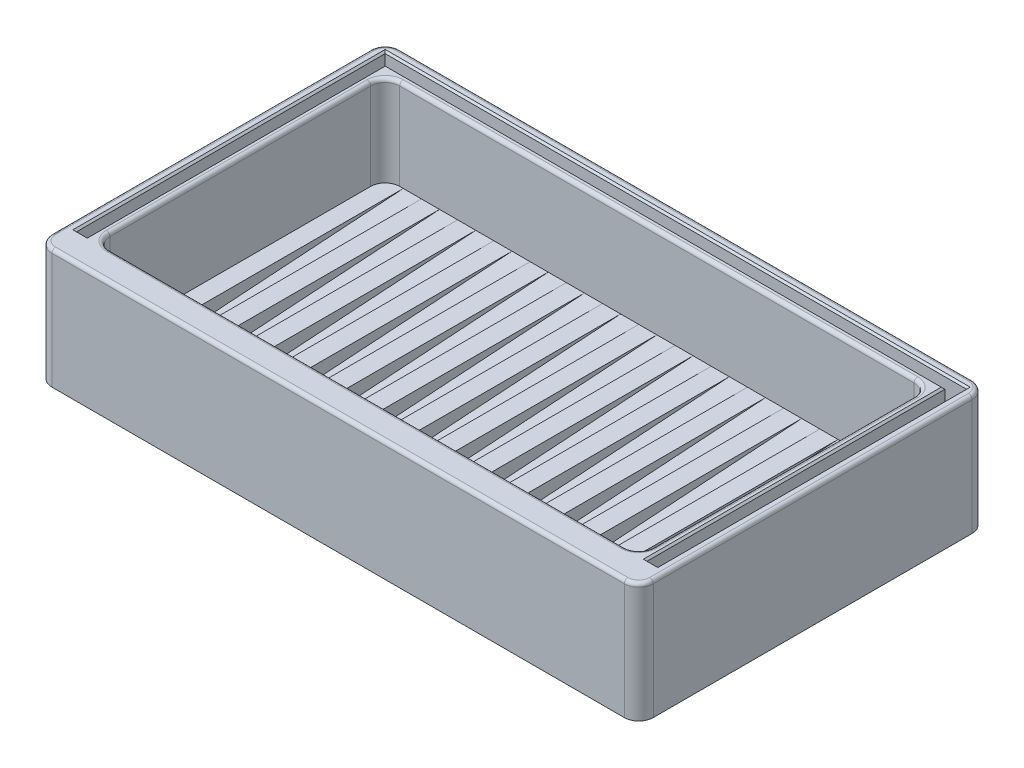
SolidWorks part; units mm, degrees
ref_plane "Front Plane" through (0, 0, 0) normal (0, 0, 1) x (1, 0, 0)
ref_plane "Top Plane" through (0, 0, 0) normal (0, 1, 0) x (1, 0, 0)
ref_plane "Right Plane" through (0, 0, 0) normal (1, 0, 0) x (0, 0, -1)
sketch "Sketch1" plane through (0, 0, 0) normal (0, 1, 0) x (1, 0, 0)
  line L1 (-64.9244, 29.2933) -> (101.0756, 29.2933)
  line L2 (-64.9244, 29.2933) -> (-64.9244, -66.7067)
  line L3 (-64.9244, -66.7067) -> (101.0756, -66.7067)
  line L4 (101.0756, 29.2933) -> (101.0756, -66.7067)
  dimension "D1" = 166
  dimension "D2" = 96
extrude "Boss-Extrude1" add sketch "Sketch1" along normal blind 33
sketch "Sketch2" plane through (0, 33, 0) normal (0, 1, 0) x (1, 0, 0)
  line L0 (101.0756, 29.2933) -> (-64.9244, 29.2933) construction
  line L1 (-56.9244, 21.2933) -> (93.0756, 21.2933)
  line L2 (-56.9244, 21.2933) -> (-56.9244, -58.7067)
  line L3 (-56.9244, -58.7067) -> (93.0756, -58.7067)
  line L4 (93.0756, 21.2933) -> (93.0756, -58.7067)
  line L5 (-64.9244, 29.2933) -> (-64.9244, -66.7067) construction
  dimension "D1" = 150
  dimension "D2" = 80
  dimension "D3" = 8
  dimension "D4" = 8
extrude "Cut-Extrude1" cut sketch "Sketch2" against normal blind 30
sketch "Sketch4" plane through (93.0756, 0, 0) normal (-1, 0, 0) x (0, 0, 1)
  line L0 (53.7067, 3) -> (-21.2933, 8)
  line L1 (58.7067, 3) -> (-21.2933, 3) construction
  line L2 (-21.2933, 8) -> (-21.2933, 3)
  line L3 (-21.2933, 3) -> (53.7067, 3)
  dimension "D1" = 5
  dimension "D2" = 5
extrude "Boss-Extrude2" add sketch "Sketch4" along normal blind 5
sketch "Sketch5" plane through (88.0756, 0, 0) normal (-1, 0, 0) x (0, 0, 1)
  line L0 (53.7067, 3) -> (53.7067, 8)
  line L1 (53.7067, 8) -> (-21.2933, 8)
  line L2 (-21.2933, 8) -> (-21.2933, 3)
  line L3 (-21.2933, 3) -> (53.7067, 3)
  dimension "D1" = 5
extrude "Boss-Extrude3" add sketch "Sketch5" along normal blind 5
pattern_linear "LPattern1" count 15 spacing 10 along (-1, 0, 0) of "Boss-Extrude2", "Boss-Extrude3"
sketch "Sketch9" plane through (0, 33, 0) normal (0, 1, 0) x (1, 0, 0)
  line L0 (101.0756, 29.2933) -> (-64.9244, 29.2933) construction
  line L1 (-62.1744, 26.5433) -> (98.3256, 26.5433)
  line L2 (-62.1744, 26.5433) -> (-62.1744, -58.7067)
  line L3 (-62.1744, -58.7067) -> (-59.1744, -58.7067)
  line L4 (98.3256, 26.5433) -> (98.3256, -58.7067)
  line L5 (-59.1744, 23.5433) -> (95.3256, 23.5433)
  line L6 (-59.1744, 23.5433) -> (-59.1744, -58.7067)
  line L8 (95.3256, 23.5433) -> (95.3256, -58.7067)
  line L9 (-64.9244, 29.2933) -> (-64.9244, -66.7067) construction
  line L10 (101.0756, -66.7067) -> (101.0756, 29.2933) construction
  line L11 (-64.9244, -66.7067) -> (101.0756, -66.7067) construction
  line L12 (95.3256, -58.7067) -> (98.3256, -58.7067)
  point P16 (0, 0)
  point P17 (0, 0)
  dimension "D1" = 3
  dimension "D2" = 3
  dimension "D4" = 3
  dimension "D5" = 2.75
  dimension "D6" = 2.75
  dimension "D7" = 2.75
  dimension "D8" = 8
extrude "Cut-Extrude5" cut sketch "Sketch9" against normal blind 10
fillet "Fillet1" radius 4 4 edges at (-64.9244, 16.5, -29.2933) (101.0756, 16.5, -29.2933) (101.0756, 16.5, 66.7067) (-64.9244, 16.5, 66.7067)
fillet "Fillet2" radius 4 4 edges at (93.0756, 18, 58.7067) (93.0756, 20.5, -21.2933) (-56.9244, 20.5, -21.2933) (-56.9244, 18, 58.7067)
fillet "Fillet3" radius 2 15 edges at (85.5756, 8, 53.7067) (75.5756, 8, 53.7067) (65.5756, 8, 53.7067) (55.5756, 8, 53.7067) (45.5756, 8, 53.7067) (35.5756, 8, 53.7067) (25.5756, 8, 53.7067) (15.5756, 8, 53.7067) (5.5756, 8, 53.7067) (-4.4244, 8, 53.7067) (-14.4244, 8, 53.7067) (-24.4244, 8, 53.7067) (-34.4244, 8, 53.7067) (-44.4244, 8, 53.7067) (-54.4244, 8, 53.7067)
fillet "Fillet5" radius 1 16 edges at (-55.7529, 33, 57.5351) (-56.9244, 33, 18.7067) (18.0756, 33, 58.7067) (91.904, 33, 57.5351) (93.0756, 33, 18.7067) (91.904, 33, -20.1217) (18.0756, 33, -21.2933) (-55.7529, 33, -20.1217) (-63.7529, 33, -28.1217) (18.0756, 33, -29.2933) (99.904, 33, -28.1217) (101.0756, 33, 18.7067) (99.904, 33, 65.5351) (18.0756, 33, 66.7067) (-64.9244, 33, 18.7067) (-63.7529, 33, 65.5351)
chamfer "Chamfer1" distance 0.5 angle 45 8 edges at (95.3256, 33, 17.5817) (96.8256, 33, 58.7067) (98.3256, 33, 16.0817) (18.0756, 33, -23.5433) (-59.1744, 33, 17.5817) (-60.6744, 33, 58.7067) (-62.1744, 33, 16.0817) (18.0756, 33, -26.5433)
equation "\"Inner width\"= 80"
equation "\"Inner length\" = 150"
equation "\"pannel thick\" = 2.5"
equation "\"base thickness\" = 3"
equation "\"D1@Sketch1\" = \"Inner length\" + \"Side thickness\" * 2"
equation "\"D2@Sketch1\" = \"Inner width\" + \"Side thickness\" * 2"
equation "\"Base inner height\"= 25"
equation "\"D1@Boss-Extrude1\"=\"Base inner height\"+\"base thickness\"+\"Drainage height\""
equation "\"D1@Sketch2\"=\"Inner length\""
equation "\"D2@Sketch2\"=\"Inner width\""
equation "\"D3@Sketch2\"=\"Side thickness\""
equation "\"D4@Sketch2\" = \"Side thickness\""
equation "\"Drainage height\" = 5"
equation "\"D1@Cut-Extrude1\"=\"Base inner height\"+\"Drainage height\""
equation "\"Side thickness\" = 8"
equation "\"D1@Sketch4\"=\"Drainage height\""
equation "\"Drainage gap\"= \"Inner length\" / \"Drain amount\""
equation "\"D2@Sketch4\"=\"Drainage gap\""
equation "\"D1@Boss-Extrude2\"=\"Drainage gap\""
equation "\"D1@Sketch5\"=\"Drainage height\""
equation "\"D3@LPattern1\"=\"Drainage gap\"*2"
equation "\"Drain amount\"= 30"
equation "\"pannel seat depth\"= 10"
equation "\"D1@Cut-Extrude5\"=\"pannel seat depth\""
equation "\"D8@Sketch9\"=\"Side thickness\""
equation "\"D1@Boss-Extrude3\"=\"Drainage gap\""
equation "\"D6@Sketch9\"=(\"Side thickness\"-\"pannel thick\")/2"
equation "\"D7@Sketch9\"=(\"Side thickness\"-\"pannel thick\")/2"
equation "\"D5@Sketch9\"=(\"Side thickness\"-\"pannel thick\")/2"
